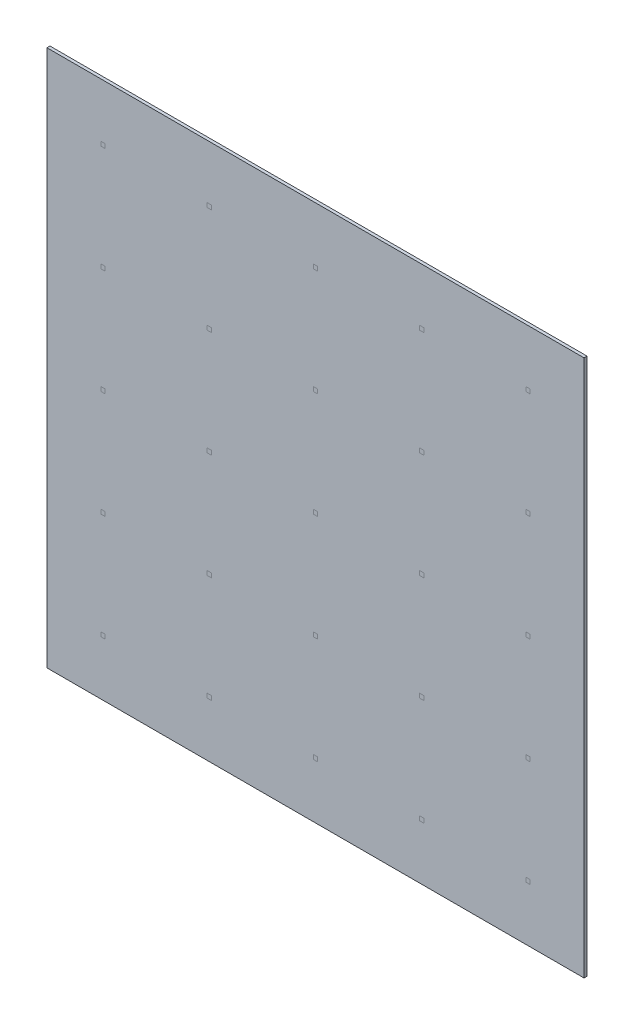
SolidWorks part; units mm, degrees
ref_plane "Front Plane" through (0, 0, 0) normal (0, 0, 1) x (1, 0, 0)
ref_plane "Top Plane" through (0, 0, 0) normal (0, 1, 0) x (1, 0, 0)
ref_plane "Right Plane" through (0, 0, 0) normal (1, 0, 0) x (0, 0, -1)
sketch "Sketch7" plane through (0, 0, 0) normal (0, 0, 1) x (1, 0, 0)
  line L0 (0, 2.2) -> (4.4, 2.2) construction
  line L1 (0, 0) -> (4.4, 0) construction
  line L2 (0, 0) -> (0, 4.4) construction
  line L3 (0, 4.4) -> (4.4, 4.4) construction
  line L4 (4.4, 0) -> (4.4, 4.4) construction
  line L5 (4.4, 4.4) -> (3.52, 4.4) construction
  line L6 (4.4, 4.4) -> (4.4, 3.52) construction
  line L7 (4.4, 3.52) -> (3.52, 3.52) construction
  line L8 (3.52, 4.4) -> (3.52, 3.52) construction
  line L9 (0, 4.4) -> (0.88, 4.4) construction
  line L10 (0, 4.4) -> (0, 3.52) construction
  line L11 (0, 3.52) -> (0.88, 3.52) construction
  line L12 (0.88, 4.4) -> (0.88, 3.52) construction
  line L13 (4.4, 0) -> (3.52, 0) construction
  line L14 (4.4, 0) -> (4.4, 0.88) construction
  line L15 (4.4, 0.88) -> (3.52, 0.88) construction
  line L16 (3.52, 0) -> (3.52, 0.88) construction
  line L17 (0, 0) -> (0.88, 0) construction
  line L18 (0, 0) -> (0, 0.88) construction
  line L19 (0, 0.88) -> (0.88, 0.88) construction
  line L20 (0.88, 0) -> (0.88, 0.88) construction
  line L21 (-0.025, -0.025) -> (4.425, -0.025)
  line L22 (-0.025, -0.025) -> (-0.025, 4.425)
  line L23 (-0.025, 4.425) -> (4.425, 4.425)
  line L24 (4.425, -0.025) -> (4.425, 4.425)
  line L25 (-0.025, -0.025) -> (4.425, 4.425) construction
  line L26 (-0.025, 4.425) -> (4.425, -0.025) construction
  point P17 (2.2, 2.2)
  dimension "D1" = 0.88
  dimension "D2" = 4.4
  dimension "D3" = 0.025
sketch "Sketch10" plane through (0, 0, 0) normal (0, 0, 1) x (1, 0, 0)
  line L16 (0.88, 0.88) -> (0, 0) construction
  line L17 (0, 0) -> (0.88, 0) construction
  line L103 (0, 0) -> (0, 0.88) construction
  line L104 (0, 0.88) -> (0.88, 0.88) construction
  line L105 (0.88, 0) -> (0.88, 0.88) construction
  line L106 (0.4222, 0.4222) -> (0.4578, 0.4222)
  line L107 (0.4222, 0.4222) -> (0.4222, 0.4578)
  line L108 (0.4222, 0.4578) -> (0.4578, 0.4578)
  line L109 (0.4578, 0.4222) -> (0.4578, 0.4578)
  line L110 (0.4222, 0.4222) -> (0.4578, 0.4578) construction
  line L111 (0.4222, 0.4578) -> (0.4578, 0.4222) construction
  line L112 (1.3022, 0.4222) -> (1.3378, 0.4222)
  line L113 (1.3378, 0.4222) -> (1.3378, 0.4578)
  line L114 (1.3022, 0.4578) -> (1.3378, 0.4578)
  line L115 (1.3022, 0.4222) -> (1.3022, 0.4578)
  line L116 (1.3022, 1.3022) -> (1.3378, 1.3022)
  line L117 (1.3378, 1.3022) -> (1.3378, 1.3378)
  line L118 (1.3022, 1.3378) -> (1.3378, 1.3378)
  line L119 (1.3022, 1.3022) -> (1.3022, 1.3378)
  line L120 (0.4222, 1.3022) -> (0.4578, 1.3022)
  line L121 (0.4578, 1.3022) -> (0.4578, 1.3378)
  line L122 (0.4222, 1.3378) -> (0.4578, 1.3378)
  line L123 (0.4222, 1.3022) -> (0.4222, 1.3378)
  line L124 (0.4222, 0.4222) -> (1.3022, 0.4222) construction
  line L125 (0.4222, 0.4222) -> (0.4222, 1.3022) construction
  line L126 (2.1822, 0.4222) -> (2.2178, 0.4222)
  line L127 (2.2178, 0.4222) -> (2.2178, 0.4578)
  line L128 (2.1822, 0.4578) -> (2.2178, 0.4578)
  line L129 (2.1822, 0.4222) -> (2.1822, 0.4578)
  line L130 (3.0622, 0.4222) -> (3.0978, 0.4222)
  line L131 (3.0978, 0.4222) -> (3.0978, 0.4578)
  line L132 (3.0622, 0.4578) -> (3.0978, 0.4578)
  line L133 (3.0622, 0.4222) -> (3.0622, 0.4578)
  line L134 (3.9422, 0.4222) -> (3.9778, 0.4222)
  line L135 (3.9778, 0.4222) -> (3.9778, 0.4578)
  line L136 (3.9422, 0.4578) -> (3.9778, 0.4578)
  line L137 (3.9422, 0.4222) -> (3.9422, 0.4578)
  line L138 (2.1822, 1.3022) -> (2.2178, 1.3022)
  line L139 (2.2178, 1.3022) -> (2.2178, 1.3378)
  line L140 (2.1822, 1.3378) -> (2.2178, 1.3378)
  line L141 (2.1822, 1.3022) -> (2.1822, 1.3378)
  line L142 (3.0622, 1.3022) -> (3.0978, 1.3022)
  line L143 (3.0978, 1.3022) -> (3.0978, 1.3378)
  line L144 (3.0622, 1.3378) -> (3.0978, 1.3378)
  line L145 (3.0622, 1.3022) -> (3.0622, 1.3378)
  line L146 (3.9422, 1.3022) -> (3.9778, 1.3022)
  line L147 (3.9778, 1.3022) -> (3.9778, 1.3378)
  line L148 (3.9422, 1.3378) -> (3.9778, 1.3378)
  line L149 (3.9422, 1.3022) -> (3.9422, 1.3378)
  line L150 (0.4222, 2.1822) -> (0.4578, 2.1822)
  line L151 (0.4578, 2.1822) -> (0.4578, 2.2178)
  line L152 (0.4222, 2.2178) -> (0.4578, 2.2178)
  line L153 (0.4222, 2.1822) -> (0.4222, 2.2178)
  line L154 (1.3022, 2.1822) -> (1.3378, 2.1822)
  line L155 (1.3378, 2.1822) -> (1.3378, 2.2178)
  line L156 (1.3022, 2.2178) -> (1.3378, 2.2178)
  line L157 (1.3022, 2.1822) -> (1.3022, 2.2178)
  line L158 (2.1822, 2.1822) -> (2.2178, 2.1822)
  line L159 (2.2178, 2.1822) -> (2.2178, 2.2178)
  line L160 (2.1822, 2.2178) -> (2.2178, 2.2178)
  line L161 (2.1822, 2.1822) -> (2.1822, 2.2178)
  line L162 (3.0622, 2.1822) -> (3.0978, 2.1822)
  line L163 (3.0978, 2.1822) -> (3.0978, 2.2178)
  line L164 (3.0622, 2.2178) -> (3.0978, 2.2178)
  line L165 (3.0622, 2.1822) -> (3.0622, 2.2178)
  line L166 (3.9422, 2.1822) -> (3.9778, 2.1822)
  line L167 (3.9778, 2.1822) -> (3.9778, 2.2178)
  line L168 (3.9422, 2.2178) -> (3.9778, 2.2178)
  line L169 (3.9422, 2.1822) -> (3.9422, 2.2178)
  line L170 (0.4222, 3.0622) -> (0.4578, 3.0622)
  line L171 (0.4578, 3.0622) -> (0.4578, 3.0978)
  line L172 (0.4222, 3.0978) -> (0.4578, 3.0978)
  line L173 (0.4222, 3.0622) -> (0.4222, 3.0978)
  line L174 (1.3022, 3.0622) -> (1.3378, 3.0622)
  line L175 (1.3378, 3.0622) -> (1.3378, 3.0978)
  line L176 (1.3022, 3.0978) -> (1.3378, 3.0978)
  line L177 (1.3022, 3.0622) -> (1.3022, 3.0978)
  line L178 (2.1822, 3.0622) -> (2.2178, 3.0622)
  line L179 (2.2178, 3.0622) -> (2.2178, 3.0978)
  line L180 (2.1822, 3.0978) -> (2.2178, 3.0978)
  line L181 (2.1822, 3.0622) -> (2.1822, 3.0978)
  line L182 (3.0622, 3.0622) -> (3.0978, 3.0622)
  line L183 (3.0978, 3.0622) -> (3.0978, 3.0978)
  line L184 (3.0622, 3.0978) -> (3.0978, 3.0978)
  line L185 (3.0622, 3.0622) -> (3.0622, 3.0978)
  line L186 (3.9422, 3.0622) -> (3.9778, 3.0622)
  line L187 (3.9778, 3.0622) -> (3.9778, 3.0978)
  line L188 (3.9422, 3.0978) -> (3.9778, 3.0978)
  line L189 (3.9422, 3.0622) -> (3.9422, 3.0978)
  line L190 (0.4222, 3.9422) -> (0.4578, 3.9422)
  line L191 (0.4578, 3.9422) -> (0.4578, 3.9778)
  line L192 (0.4222, 3.9778) -> (0.4578, 3.9778)
  line L193 (0.4222, 3.9422) -> (0.4222, 3.9778)
  line L194 (1.3022, 3.9422) -> (1.3378, 3.9422)
  line L195 (1.3378, 3.9422) -> (1.3378, 3.9778)
  line L196 (1.3022, 3.9778) -> (1.3378, 3.9778)
  line L197 (1.3022, 3.9422) -> (1.3022, 3.9778)
  line L198 (2.1822, 3.9422) -> (2.2178, 3.9422)
  line L199 (2.2178, 3.9422) -> (2.2178, 3.9778)
  line L200 (2.1822, 3.9778) -> (2.2178, 3.9778)
  line L201 (2.1822, 3.9422) -> (2.1822, 3.9778)
  line L202 (3.0622, 3.9422) -> (3.0978, 3.9422)
  line L203 (3.0978, 3.9422) -> (3.0978, 3.9778)
  line L204 (3.0622, 3.9778) -> (3.0978, 3.9778)
  line L205 (3.0622, 3.9422) -> (3.0622, 3.9778)
  line L206 (3.9422, 3.9422) -> (3.9778, 3.9422)
  line L207 (3.9778, 3.9422) -> (3.9778, 3.9778)
  line L208 (3.9422, 3.9778) -> (3.9778, 3.9778)
  line L209 (3.9422, 3.9422) -> (3.9422, 3.9778)
  point P4 (0.44, 0.44)
  dimension "D1" = 0.88
  dimension "D2" = 0.0355
  dimension "D5" = 0.88
  dimension "D6" = 0.88
  dimension "D3" = 5
  dimension "D4" = 5
extrude "Boss-Extrude1" add sketch "Sketch7" along normal blind 0.025
split line "Split Line3"
equation "\"SQ_WIDTH\"= ( \"Apature_Size\" ) / \"Squares_per_side\""
equation "\"Total_Squares\"= 25"
equation "\"D1@Sketch7\"=\"SQ_WIDTH\""
equation "\"THK\"= 0.025"
equation "\"Squares_per_side\"= 5'\"Change For mesh size\""
equation "\"Apature_Size\"= 4.4mm'\"From Thor Labs\""
equation "\"D2@Sketch7\"=\"Apature_Size\""
equation "\"D3@Sketch7\"=\"THK\""
equation "\"D1@Sketch10\"=\"SQ_WIDTH\""
equation "\"Post_width\"= 0.0403768506 * \"SQ_WIDTH\""
equation "\"D2@Sketch10\"=\"Post_width\""
equation "\"D5@Sketch10\"= \"SQ_WIDTH\""
equation "\"D6@Sketch10\"= \"SQ_WIDTH\""
equation "\"D3@Sketch10\"= \"Squares_per_side\""
equation "\"D4@Sketch10\"= \"Squares_per_side\""
equation "\"D1@Boss-Extrude1\"=\"THK\""
